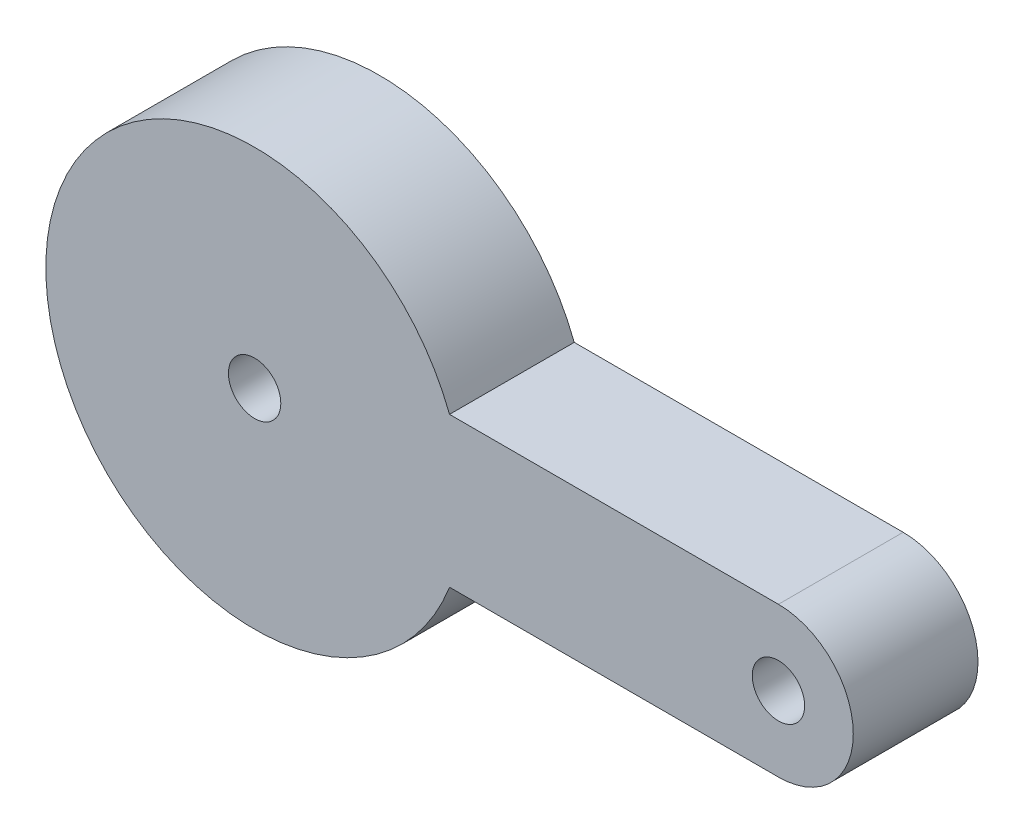
SolidWorks part; units mm, degrees
ref_plane "Front Plane" through (0, 0, 0) normal (0, 0, 1) x (1, 0, 0)
ref_plane "Top Plane" through (0, 0, 0) normal (0, 1, 0) x (1, 0, 0)
ref_plane "Right Plane" through (0, 0, 0) normal (1, 0, 0) x (0, 0, -1)
sketch "Sketch1" plane through (0, 0, 0) normal (0, 0, 1) x (1, 0, 0)
  line L0 (0, 0) -> (35, 0) construction
  line L1 (35, 5) -> (13.0232, 5)
  line L2 (35, -5) -> (13.0232, -5)
  arc A0 (13.0232, 5) -> (13.0232, -5) centre (0, 0) ccw
  arc A1 (35, -5) -> (35, 5) centre (35, 0) ccw
  circle A2 centre (0, 0) radius 1.75
  circle A3 centre (35, 0) radius 1.75
  dimension "D2" = 27.9
  dimension "D3" = 10
  dimension "D4" = 3.5
  dimension "D5" = 3.5
  dimension "D1" = 35
extrude "Boss-Extrude1" add sketch "Sketch1" along normal blind 8.3333
